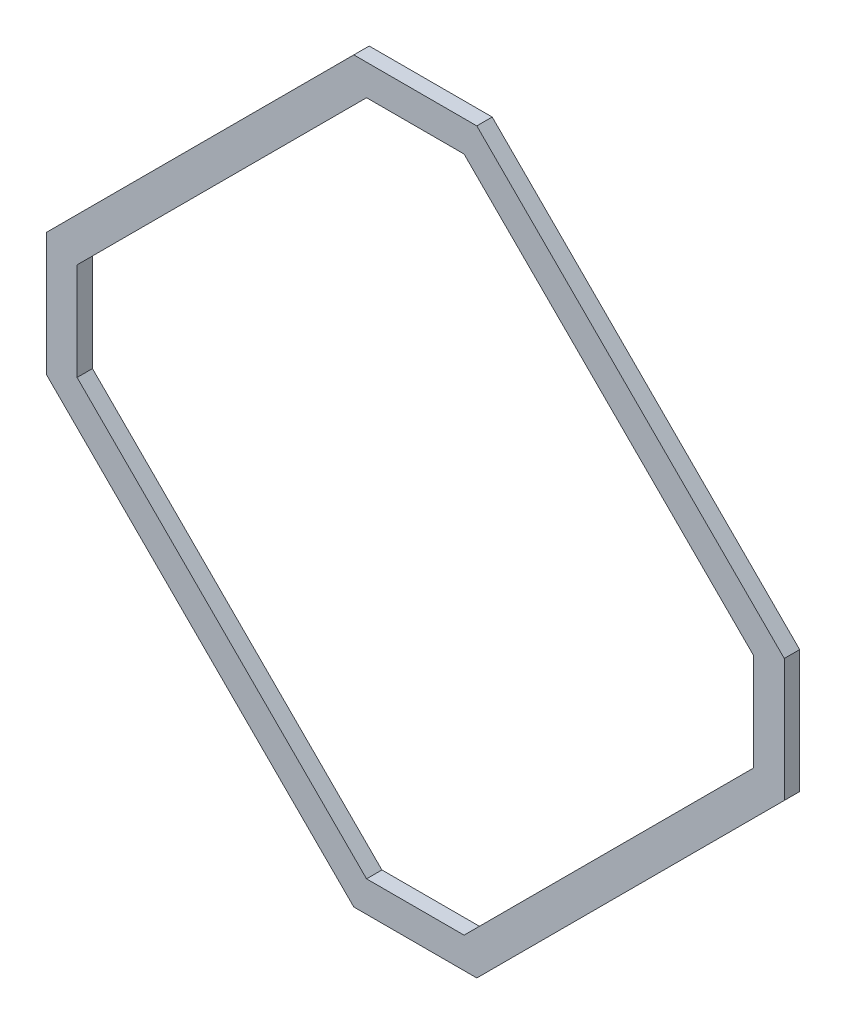
SolidWorks part; units mm, degrees
material "1060 Alloy"
ref_plane "Front Plane" through (0, 0, 0) normal (0, 0, 1) x (1, 0, 0)
ref_plane "Top Plane" through (0, 0, 0) normal (0, 1, 0) x (1, 0, 0)
ref_plane "Right Plane" through (0, 0, 0) normal (1, 0, 0) x (0, 0, -1)
sketch "Sketch1" plane through (0, 0, 0) normal (0, 0, 1) x (1, 0, 0)
  line L0 (63.5, -78.5114) -> (0, -15.0114) construction
  line L1 (63.5, -103.9114) -> (63.5, -78.5114) construction
  line L2 (0, -167.4114) -> (63.5, -103.9114) construction
  line L3 (-25.4, -167.4114) -> (0, -167.4114) construction
  line L4 (-88.9, -103.9114) -> (-25.4, -167.4114) construction
  line L5 (-88.9, -78.5114) -> (-88.9, -103.9114) construction
  line L6 (-25.4, -15.0114) -> (-88.9, -78.5114) construction
  line L7 (0, -15.0114) -> (-25.4, -15.0114) construction
  line L8 (63.5, -78.5114) -> (0, -15.0114)
  line L9 (63.5, -103.9114) -> (63.5, -78.5114)
  line L10 (0, -167.4114) -> (63.5, -103.9114)
  line L11 (-25.4, -167.4114) -> (0, -167.4114)
  line L12 (-88.9, -103.9114) -> (-25.4, -167.4114)
  line L13 (-88.9, -78.5114) -> (-88.9, -103.9114)
  line L14 (-25.4, -15.0114) -> (-88.9, -78.5114)
  line L15 (0, -15.0114) -> (-25.4, -15.0114)
  line L16 (57.15, -81.1417) -> (-2.6303, -21.3614)
  line L17 (-2.6303, -21.3614) -> (-22.7697, -21.3614)
  line L18 (-22.7697, -21.3614) -> (-82.55, -81.1417)
  line L19 (-82.55, -81.1417) -> (-82.55, -101.2811)
  line L20 (-82.55, -101.2811) -> (-22.7697, -161.0614)
  line L21 (-22.7697, -161.0614) -> (-2.6303, -161.0614)
  line L22 (-2.6303, -161.0614) -> (57.15, -101.2811)
  line L23 (57.15, -101.2811) -> (57.15, -81.1417)
  dimension "D1" = 6.35
extrude "Boss-Extrude1" add sketch "Sketch1" along normal blind 3.175 contours L16 L17 L18 L19 L20 L21 L22 L23 | L8 L15 L14 L13 L12 L11 L10 L9
